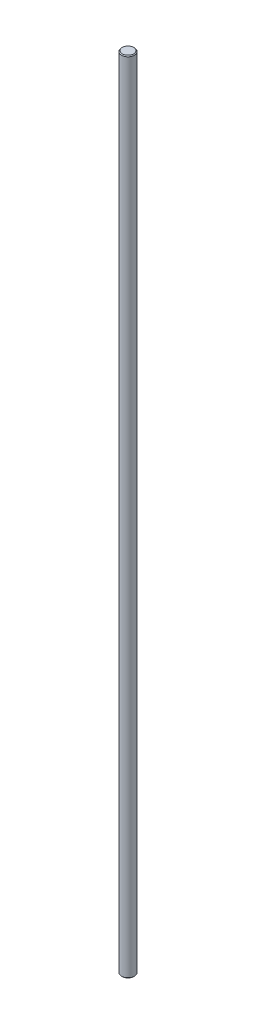
SolidWorks part; units mm, degrees
ref_plane "Front Plane" through (0, 0, 0) normal (0, 0, 1) x (1, 0, 0)
ref_plane "Top Plane" through (0, 0, 0) normal (0, 1, 0) x (1, 0, 0)
ref_plane "Right Plane" through (0, 0, 0) normal (1, 0, 0) x (0, 0, -1)
sketch "Sketch1" plane through (0, 0, 0) normal (0, 1, 0) x (1, 0, 0)
  circle A0 centre (0, 0) radius 4
  dimension "D1" = 8
extrude "Boss-Extrude1" add sketch "Sketch1" along normal blind 495.3
chamfer "Chamfer1" distance 0.5 angle 45 2 edges at (0, 0, 4) (0, 495.3, 4)
